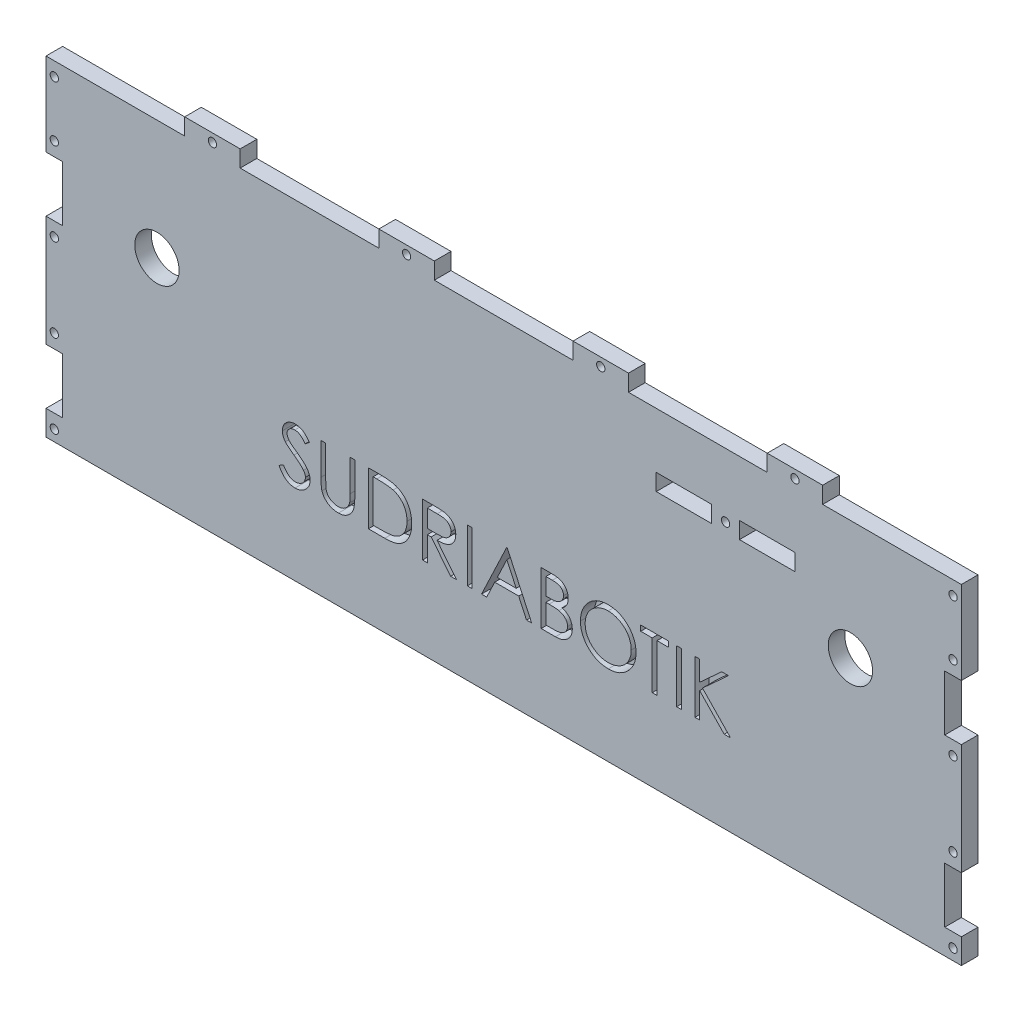
SolidWorks part; units mm, degrees
ref_plane "Plan de face" through (0, 0, 0) normal (0, 0, 1) x (1, 0, 0)
ref_plane "Plan de dessus" through (0, 0, 0) normal (0, 1, 0) x (1, 0, 0)
ref_plane "Plan de droite" through (0, 0, 0) normal (1, 0, 0) x (0, 0, -1)
sketch "Esquisse1" plane through (0, 0, 0) normal (0, 0, 1) x (1, 0, 0)
  line L0 (97.3951, 0) -> (-118.5049, 0) construction
  line L1 (-165, 119) -> (165, 119)
  line L2 (-165, 119) -> (-165, -119)
  line L3 (-165, -119) -> (165, -119)
  line L4 (165, 119) -> (165, -119)
  line L5 (0, 79.3588) -> (0, -79.3588) construction
  line L6 (-92.5, -55) -> (-77.5, -55)
  line L7 (-92.5, -55) -> (-92.5, -61)
  line L8 (-92.5, -61) -> (-77.5, -61)
  line L9 (-77.5, -55) -> (-77.5, -61)
  line L10 (-7.5, -55) -> (7.5, -55)
  line L11 (-7.5, -55) -> (-7.5, -61)
  line L12 (-7.5, -61) -> (7.5, -61)
  line L13 (7.5, -55) -> (7.5, -61)
  line L14 (77.5, -55) -> (92.5, -55)
  line L15 (77.5, -55) -> (77.5, -61)
  line L16 (77.5, -61) -> (92.5, -61)
  line L17 (92.5, -55) -> (92.5, -61)
  line L18 (-225.3679, 76) -> (203.1013, 76) construction
  line L19 (55, 99) -> (75, 99)
  line L20 (55, 99) -> (55, 93)
  line L21 (55, 93) -> (75, 93)
  line L22 (75, 99) -> (75, 93)
  line L23 (85, 99) -> (105, 99)
  line L24 (85, 99) -> (85, 93)
  line L25 (85, 93) -> (105, 93)
  line L26 (105, 99) -> (105, 93)
  circle A0 centre (-125, 76) radius 8
  circle A1 centre (125, 76) radius 8
  dimension "D23" = 16
  dimension "D24" = 16
  dimension "D1" = 238
  dimension "D2" = 330
  dimension "D3" = 165
  dimension "D4" = 119
  dimension "D5" = 15
  dimension "D6" = 6
  dimension "D7" = 6
  dimension "D8" = 15
  dimension "D9" = 6
  dimension "D10" = 15
  dimension "D11" = 70
  dimension "D12" = 70
  dimension "D13" = 58
  dimension "D14" = 72.5
  dimension "D15" = 6
  dimension "D16" = 20
  dimension "D17" = 20
  dimension "D18" = 6
  dimension "D19" = 10
  dimension "D20" = 60
  dimension "D21" = 20
  dimension "D22" = 20
  dimension "D25" = 40
  dimension "D26" = 40
  dimension "D27" = 195
extrude "Boss.-Extru.1" add sketch "Esquisse1" along normal blind 6
sketch "Esquisse2" plane through (0, 0, 6) normal (0, 0, 1) x (1, 0, 0)
  line L0 (243.146, 0) -> (-260.0003, 0) construction
  line L1 (0, 180.4713) -> (0, -129.6072) construction
  line L2 (165, 119) -> (-165, 119) construction
  line L3 (-115, 119) -> (-95, 119)
  line L4 (-115, 119) -> (-115, 125)
  line L5 (-115, 125) -> (-95, 125)
  line L6 (-95, 119) -> (-95, 125)
  line L7 (-165, 119) -> (-165, -119) construction
  line L8 (-45, 119) -> (-25, 119)
  line L9 (-45, 119) -> (-45, 125)
  line L10 (-45, 125) -> (-25, 125)
  line L11 (-25, 119) -> (-25, 125)
  line L12 (25, 119) -> (25, 125)
  line L13 (45, 125) -> (25, 125)
  line L14 (45, 119) -> (45, 125)
  line L15 (45, 119) -> (25, 119)
  line L16 (95, 119) -> (95, 125)
  line L17 (115, 125) -> (95, 125)
  line L18 (115, 119) -> (115, 125)
  line L19 (115, 119) -> (95, 119)
  line L20 (-115, 119) -> (-95, 119)
  line L21 (-115, 119) -> (-115, 125)
  line L22 (-115, 125) -> (-95, 125)
  line L23 (-95, 119) -> (-95, 125)
  line L24 (-45, 119) -> (-25, 119)
  line L25 (-45, 119) -> (-45, 125)
  line L26 (-45, 125) -> (-25, 125)
  line L27 (-25, 119) -> (-25, 125)
  line L28 (25, 119) -> (25, 125)
  line L29 (45, 125) -> (25, 125)
  line L30 (45, 119) -> (45, 125)
  line L31 (45, 119) -> (25, 119)
  line L32 (95, 119) -> (95, 125)
  line L33 (115, 125) -> (95, 125)
  line L34 (115, 119) -> (115, 125)
  line L35 (115, 119) -> (95, 119)
  line L36 (115, -119) -> (95, -119)
  line L37 (115, -119) -> (115, -125)
  line L38 (115, -125) -> (95, -125)
  line L39 (95, -119) -> (95, -125)
  line L40 (45, -119) -> (25, -119)
  line L41 (45, -119) -> (45, -125)
  line L42 (45, -125) -> (25, -125)
  line L43 (25, -119) -> (25, -125)
  line L44 (-25, -119) -> (-25, -125)
  line L45 (-45, -125) -> (-25, -125)
  line L46 (-45, -119) -> (-45, -125)
  line L47 (-45, -119) -> (-25, -119)
  line L48 (-95, -119) -> (-95, -125)
  line L49 (-115, -125) -> (-95, -125)
  line L50 (-115, -119) -> (-115, -125)
  line L51 (-115, -119) -> (-95, -119)
  line L52 (115, -119) -> (95, -119)
  line L53 (115, -119) -> (115, -125)
  line L54 (115, -125) -> (95, -125)
  line L55 (95, -119) -> (95, -125)
  line L56 (45, -119) -> (25, -119)
  line L57 (45, -119) -> (45, -125)
  line L58 (45, -125) -> (25, -125)
  line L59 (25, -119) -> (25, -125)
  line L60 (-25, -119) -> (-25, -125)
  line L61 (-45, -125) -> (-25, -125)
  line L62 (-45, -119) -> (-45, -125)
  line L63 (-45, -119) -> (-25, -119)
  line L64 (-95, -119) -> (-95, -125)
  line L65 (-115, -125) -> (-95, -125)
  line L66 (-115, -119) -> (-115, -125)
  line L67 (-115, -119) -> (-95, -119)
  line M9 (-165, -119) -> (165, -119)
  line M11 (165, 119) -> (-165, 119)
  dimension "D1" = 6
  dimension "D2" = 6
  dimension "D3" = 20
  dimension "D4" = 20
  dimension "D5" = 50
  dimension "D6" = 50
extrude "Boss.-Extru.2" add sketch "Esquisse2" against normal blind 6 contours L6 L5 L4 M11 | L11 L10 L9 M11 | L14 L13 L12 M11 | L18 L17 L16 M11 | L39 L38 L37 M9 | L43 L42 L41 M9 | L46 L45 L44 M9 | L50 L49 L48 M9
sketch "Esquisse3" plane through (0, 0, 6) normal (0, 0, 1) x (1, 0, 0)
  line L0 (-165, 119) -> (-165, -119) construction
  line L1 (-165, 69) -> (-159, 69)
  line L2 (-165, 69) -> (-165, 89)
  line L3 (-165, 89) -> (-159, 89)
  line L4 (-159, 69) -> (-159, 89)
  line L5 (234.1368, 0) -> (-337.9213, 0) construction
  line L6 (-165, 29) -> (-159, 29)
  line L7 (-165, 29) -> (-165, 9)
  line L8 (-165, 9) -> (-159, 9)
  line L9 (-159, 29) -> (-159, 9)
  line L10 (0, 279.7488) -> (0, -188.1201) construction
  line L11 (-115, 119) -> (-165, 119) construction
  line L12 (-159, -29) -> (-159, -9)
  line L13 (-165, -9) -> (-159, -9)
  line L14 (-165, -29) -> (-165, -9)
  line L15 (-165, -29) -> (-159, -29)
  line L16 (-159, -69) -> (-159, -89)
  line L17 (-165, -89) -> (-159, -89)
  line L18 (-165, -69) -> (-165, -89)
  line L19 (-165, -69) -> (-159, -69)
  line L20 (165, -69) -> (159, -69)
  line L21 (165, -69) -> (165, -89)
  line L22 (165, -89) -> (159, -89)
  line L23 (159, -69) -> (159, -89)
  line L24 (165, -29) -> (159, -29)
  line L25 (165, -29) -> (165, -9)
  line L26 (165, -9) -> (159, -9)
  line L27 (159, -29) -> (159, -9)
  line L28 (159, 29) -> (159, 9)
  line L29 (165, 9) -> (159, 9)
  line L30 (165, 29) -> (165, 9)
  line L31 (165, 29) -> (159, 29)
  line L32 (159, 69) -> (159, 89)
  line L33 (165, 89) -> (159, 89)
  line L34 (165, 69) -> (165, 89)
  line L35 (165, 69) -> (159, 69)
  line L36 (153, -119) -> (153, -109)
  line L37 (-165, -119) -> (-153, -119)
  line L38 (-165, -119) -> (-165, -109)
  line L39 (-165, -109) -> (-153, -109)
  line L40 (-153, -119) -> (-153, -109)
  line L41 (165, -109) -> (153, -109)
  line L42 (165, -119) -> (165, -109)
  line L43 (165, -119) -> (153, -119)
  dimension "D1" = 40
  dimension "D2" = 6
  dimension "D3" = 6
  dimension "D4" = 20
  dimension "D5" = 20
  dimension "D6" = 30
  dimension "D7" = 12
  dimension "D8" = 10
extrude "Enlèv. mat.-Extru.1" cut sketch "Esquisse3" against normal blind 6
sketch "Esquisse4" plane through (0, 0, 6) normal (0, 0, 1) x (1, 0, 0)
  line L0 (-162, 122) -> (-162, -131.0602) construction
  line L1 (0, 158.5579) -> (0, -182.4489) construction
  line L2 (-115, 119) -> (-165, 119) construction
  line L3 (-106.4439, -58) -> (117.3944, -58) construction
  line L4 (-159, 89) -> (-165, 89) construction
  line L5 (-165, 119) -> (-165, 89) construction
  line L6 (-165, 69) -> (-159, 69) construction
  line L7 (-159, 29) -> (-165, 29) construction
  line L8 (-165, 9) -> (-159, 9) construction
  line L9 (-159, -9) -> (-165, -9) construction
  line L10 (-92.5, -55) -> (-92.5, -61) construction
  line L11 (-77.5, -61) -> (-77.5, -55) construction
  line L12 (-165, -29) -> (-159, -29) construction
  line L13 (-159, -69) -> (-165, -69) construction
  line L14 (-165, -89) -> (-159, -89) construction
  line L15 (-7.5, -55) -> (-7.5, -61) construction
  line L16 (162, 122) -> (162, -131.0602) construction
  line L17 (116.5184, 96) -> (43.4816, 96) construction
  line L18 (-126.5544, 122) -> (2.7821, 122) construction
  line L19 (-45, 119) -> (-95, 119) construction
  line L20 (-45, 119) -> (-45, 125) construction
  line L21 (75, 93) -> (75, 99) construction
  line L23 (55, 93) -> (75, 93) construction
  circle A0 centre (-162, 114) radius 1.5
  circle A1 centre (-162, 94) radius 1.5
  circle A2 centre (-162, 64) radius 1.5
  circle A3 centre (-162, 34) radius 1.5
  circle A4 centre (-162, 4) radius 1.5
  circle A5 centre (-105, 122) radius 1.5
  circle A6 centre (-162, -4) radius 1.5
  circle A7 centre (-162, -34) radius 1.5
  circle A8 centre (-162, -64) radius 1.5
  circle A9 centre (-162, -94) radius 1.5
  circle A10 centre (-97.5, -58) radius 1.5
  circle A11 centre (-72.5, -58) radius 1.5
  circle A12 centre (162, -94) radius 1.5
  circle A13 centre (162, -64) radius 1.5
  circle A14 centre (162, -34) radius 1.5
  circle A15 centre (162, -4) radius 1.5
  circle A16 centre (80, 96) radius 1.5
  circle A17 centre (162, 4) radius 1.5
  circle A18 centre (162, 34) radius 1.5
  circle A19 centre (162, 64) radius 1.5
  circle A20 centre (162, 94) radius 1.5
  circle A21 centre (162, 114) radius 1.5
  circle A22 centre (-12.5, -58) radius 1.5
  circle A23 centre (12.5, -58) radius 1.5
  circle A24 centre (72.5, -58) radius 1.5
  circle A25 centre (97.5, -58) radius 1.5
  circle A26 centre (-35, 122) radius 1.5
  circle A27 centre (35, 122) radius 1.5
  circle A28 centre (105, 122) radius 1.5
  dimension "D1" = 3
  dimension "D2" = 3
  dimension "D3" = 3
  dimension "D4" = 3
  dimension "D5" = 3
  dimension "D6" = 3
  dimension "D7" = 3
  dimension "D8" = 3
  dimension "D9" = 3
  dimension "D10" = 3
  dimension "D11" = 3
  dimension "D12" = 5
  dimension "D13" = 5
  dimension "D15" = 5
  dimension "D16" = 5
  dimension "D17" = 5
  dimension "D19" = 3
  dimension "D20" = 5
  dimension "D21" = 5
  dimension "D23" = 3
  dimension "D24" = 3
  dimension "D25" = 5
  dimension "D26" = 5
  dimension "D27" = 5
  dimension "D28" = 10
  dimension "D29" = 3
  dimension "D30" = 5
  dimension "D31" = 3
  dimension "D33" = 10
  dimension "D14" = 3
  dimension "D18" = 5
  dimension "D22" = 5
  dimension "D32" = 3
extrude "Enlèv. mat.-Extru.2" cut sketch "Esquisse4" against normal blind 6
sketch "Esquisse5" plane through (0, 0, 6) normal (0, 0, 1) x (1, 0, 0)
  line L1 (-200.0968, 0) -> (223.5072, 0)
  line L2 (-200.0968, 0) -> (-200.0968, -150.3561)
  line L3 (-200.0968, -150.3561) -> (223.5072, -150.3561)
  line L4 (223.5072, 0) -> (223.5072, -150.3561)
extrude "Enlèv. mat.-Extru.3" cut sketch "Esquisse5" against normal blind 6
sketch "Esquisse6" plane through (0, 0, 6) normal (0, 0, 1) x (1, 0, 0)
  line L0 (-165, 69) -> (-165, 29) construction
  line L2 (165, 0) -> (-165, 0) construction
  text T0 "SUDRIABOTIK" font "Century Gothic" height in points 72
  dimension "D1" = 83.5
  dimension "D2" = 29.5
extrude "Enlèv. mat.-Extru.4" cut sketch "Esquisse6" against normal blind 5
equation "\"D3@Esquisse1\"=\"D2@Esquisse1\"/2"
equation "\"D4@Esquisse1\"=\"D1@Esquisse1\"/2"
